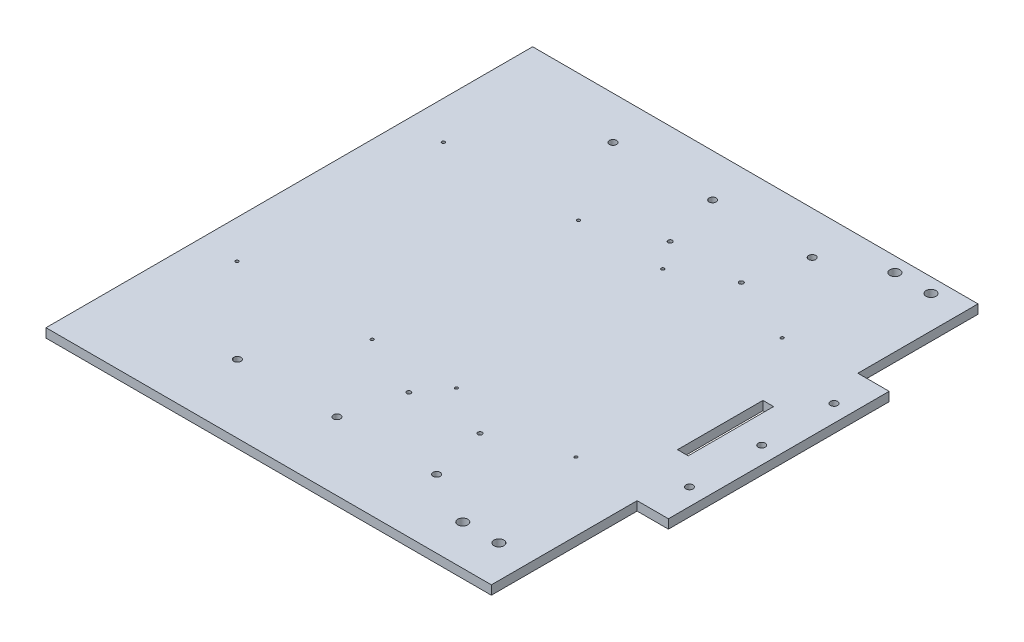
SolidWorks part; units mm, degrees
material "Cedar"
ref_plane "Front Plane" through (0, 0, 0) normal (0, 0, 1) x (1, 0, 0)
ref_plane "Top Plane" through (0, 0, 0) normal (0, 1, 0) x (1, 0, 0)
ref_plane "Right Plane" through (0, 0, 0) normal (1, 0, 0) x (0, 0, -1)
sketch "Sketch1" plane through (0, 0, 0) normal (0, 1, 0) x (1, 0, 0)
  line L0 (72.8376, -16.2766) -> (72.8376, -52.4668) construction
  line L1 (-156.5, -171) -> (156.5, -171)
  line L2 (-156.5, -171) -> (-156.5, 171)
  line L3 (-156.5, 171) -> (156.5, 171)
  line L4 (156.5, -171) -> (156.5, 171)
  line L5 (-156.5, -171) -> (156.5, 171) construction
  line L6 (-156.5, 171) -> (156.5, -171) construction
  point P0 (0, 0)
  dimension "D1" = 342
  dimension "D2" = 313
extrude "Boss-Extrude1" add sketch "Sketch1" against normal blind 6.35
ref_plane "Plane1" through (0, 0, -9) normal (0, 0, -1) x (-1, 0, 0)
sketch "Sketch3" plane through (0, 0, 0) normal (0, 1, 0) x (1, 0, 0)
  line L0 (156.5, 9) -> (-156.5, 9) construction
  line L1 (156.5, -171) -> (156.5, 171) construction
  line L2 (-156.5, 171) -> (-156.5, -171) construction
  line L3 (55, 9) -> (-55, 9) construction
  line L4 (156.5, 86.5702) -> (156.5, -68.5702)
  line L5 (156.5, -68.5702) -> (178.5, -68.5702)
  line L6 (178.5, -68.5702) -> (178.5, 86.5702)
  line L7 (178.5, 86.5702) -> (156.5, 86.5702)
  circle A0 centre (166.5, 9) radius 2.5
  circle A1 centre (166.5, -41.8) radius 2.5
  circle A2 centre (166.5, 59.8) radius 2.5
  point P10 (156.5, 9)
  dimension "D2" = 5
  dimension "D4" = 5
  dimension "D5" = 50.8
  dimension "D1" = 22
  dimension "D3" = 10
extrude "Boss-Extrude2" add sketch "Sketch3" against normal blind 6.35
sketch "Sketch2" plane through (0, 0, 0) normal (0, 1, 0) x (1, 0, 0)
  line L0 (156.5, 9) -> (-156.5, 9) construction
  line L1 (156.5, -171) -> (156.5, -68.5702) construction
  line L2 (-156.5, 171) -> (-156.5, -171) construction
  line L3 (0, -123) -> (0, -171) construction
  line L4 (55, 9) -> (-55, 9) construction
  line L5 (156.5, -123) -> (-156.5, -123) construction
  line L6 (-156.5, -171) -> (156.5, -171) construction
  circle A0 centre (0, -123) radius 2.5
  circle A1 centre (-70, -123) radius 2.5
  circle A2 centre (70, -123) radius 2.5
  circle A3 centre (-70, 141) radius 2.5
  circle A4 centre (0, 141) radius 2.5
  circle A5 centre (70, 141) radius 2.5
  dimension "D2" = 5
  dimension "D3" = 5
  dimension "D4" = 70
  dimension "D1" = 132
extrude "Cut-Extrude1" cut sketch "Sketch2" against normal through all
sketch "Sketch4" plane through (0, 0, 0) normal (0, 1, 0) x (1, 0, 0)
  line L0 (156.5, 171) -> (-156.5, 171) construction
  line L1 (156.5, 86.5702) -> (156.5, 171) construction
  circle A0 centre (133.64, 160.84) radius 3.5
  circle A1 centre (108.24, 160.84) radius 3.5
  dimension "D2" = 7
  dimension "D3" = 7
  dimension "D1" = 10.16
  dimension "D4" = 22.86
  dimension "D5" = 25.4
  dimension "D6" = 0
extrude "Cut-Extrude2" cut sketch "Sketch4" against normal through all
mirror "Mirror1" about plane through (0, 0, -9) normal (0, 0, -1) of "Cut-Extrude2"
sketch "Sketch5" plane through (0, 0, 0) normal (0, 1, 0) x (1, 0, 0)
  line L0 (139.6718, 36.6738) -> (147.1718, 36.6738)
  line L1 (147.1718, 36.6738) -> (147.1435, -23.3262)
  line L2 (147.1435, -23.3262) -> (139.6435, -23.3262)
  line L3 (139.6435, -23.3262) -> (139.6718, 36.6738)
extrude "Cut-Extrude3" cut sketch "Sketch5" against normal through all
sketch "Sketch6" plane through (0, 0, 0) normal (0, 1, 0) x (1, 0, 0)
  line L0 (68.5, 109) -> (68.5, -91) construction
  line L1 (156.5, 171) -> (-156.5, 171) construction
  line L2 (-156.5, -171) -> (156.5, -171) construction
  line L3 (156.5, -171) -> (156.5, -68.5702) construction
  line L4 (68.5, 9) -> (-108.2246, 9) construction
  line L5 (60.32, 100.82) -> (10.32, 100.82) construction
  line L6 (55, 9) -> (-55, 9) construction
  circle A0 centre (60.32, 100.82) radius 1.5
  circle A1 centre (10.32, 100.82) radius 1.5
  circle A2 centre (10.32, -82.82) radius 1.5
  circle A3 centre (60.32, -82.82) radius 1.5
  point P14 (38.3862, 105.3032)
  dimension "D4" = 3
  dimension "D5" = 3
  dimension "D1" = 62
  dimension "D2" = 80
  dimension "D3" = 88
  dimension "D6" = 50
  dimension "D7" = 8.18
  dimension "D8" = 8.18
extrude "Cut-Extrude4" cut sketch "Sketch6" against normal through all
sketch "Sketch7" plane through (0, 0, 0) normal (0, 1, 0) x (1, 0, 0)
  line L0 (-34.7429, -63.5) -> (-34.7429, 81.5) construction
  line L1 (24.4394, -63.5) -> (24.4394, 81.5) construction
  line L2 (-129.7429, -63.5) -> (-129.7429, 81.5) construction
  line L3 (108.4115, -63.5) -> (108.4115, 81.5) construction
  line L4 (55, 9) -> (-55, 9) construction
  circle A0 centre (-34.7429, 81.5) radius 1.05
  circle A1 centre (-34.7429, -63.5) radius 1.05
  circle A2 centre (-129.7429, 81.5) radius 1.05
  circle A3 centre (-129.7429, -63.5) radius 1.05
  circle A4 centre (108.4115, 81.5) radius 1.05
  circle A5 centre (108.4115, -63.5) radius 1.05
  circle A6 centre (24.4394, 81.5) radius 1.05
  circle A7 centre (24.4394, -63.5) radius 1.05
  point P16 (24.4394, 9)
  point P19 (108.4115, 9)
  point P20 (-34.7429, 9)
  point P21 (-129.7429, 9)
extrude "Cut-Extrude5" cut sketch "Sketch7" against normal through all
